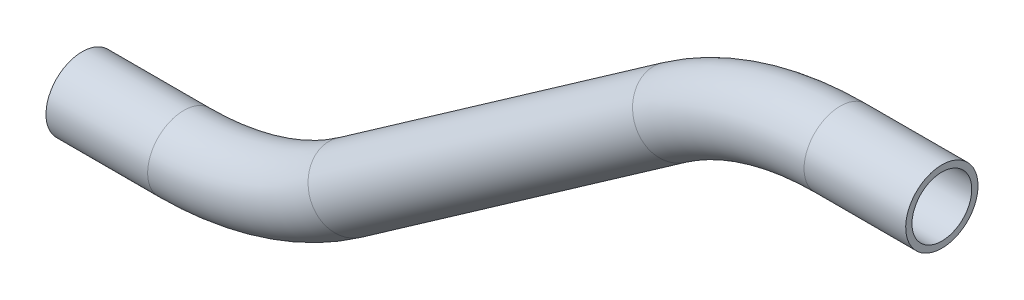
SolidWorks part; units mm, degrees
material "6061 Alloy"
ref_plane "Front Plane" through (0, 0, 0) normal (0, 0, 1) x (1, 0, 0)
ref_plane "Top Plane" through (0, 0, 0) normal (0, 1, 0) x (1, 0, 0)
ref_plane "Right Plane" through (0, 0, 0) normal (1, 0, 0) x (0, 0, -1)
sketch "Sketch4" plane through (0, 0, 0) normal (0, 0, 1) x (1, 0, 0)
  line L0 (95.0917, 47.4325) -> (121.8659, 47.4325)
  line L2 (51.3852, 33.6519) -> (-34.0921, -26.1999)
  line L3 (-34.0921, -26.1999) -> (71.0659, 47.4325)
  line L4 (121.8659, 47.4325) -> (71.0659, 47.4325)
  line L5 (-77.7986, -39.9805) -> (-104.5728, -39.9805)
  line L6 (-104.5728, -39.9805) -> (-53.7728, -39.9805)
  line L7 (51.3852, 33.6519) -> (-53.7728, -39.9805)
  arc A0 (95.0917, 47.4325) -> (51.3852, 33.6519) centre (95.0917, -28.7675) ccw
  arc A1 (-34.0921, -26.1999) -> (-77.7986, -39.9805) centre (-77.7986, 36.2195) cw
  point P9 (71.0659, 47.4325)
  point P14 (-53.7728, -39.9805)
  dimension "D3" = 35
  dimension "D4" = 35
  dimension "D1" = 76.2
  dimension "D2" = 76.2
  dimension "D5" = 152.4
  dimension "D6" = 50.8
  dimension "D7" = 50.8
ref_plane "Plane2" through (121.8659, 47.4325, 0) normal (-1, 0, 0) x (0, 0, 1)
sketch "Sketch5" plane through (121.8659, 47.4325, 0) normal (-1, 0, 0) x (0, 0, 1)
  circle A0 centre (0, 0) radius 9.525
  circle A1 centre (0, 0) radius 7.874
  dimension "D1" = 15.748
  dimension "D2" = 19.05
sweep "Sweep1" add profiles "Sketch5" path "Sketch4"
sketch "Sketch6" plane through (-104.5728, 0, 0) normal (-1, 0, 0) x (0, 0, 1)
  line L0 (-7.874, -39.9805) -> (7.874, -39.9805) construction
sketch "Sketch7" plane through (0, 0, 0) normal (0, 0, 1) x (1, 0, 0)
  line L0 (-104.5728, -39.9805) -> (-136.2487, -39.9805) construction
  line L1 (-104.5728, -30.4555) -> (-104.5728, -49.5055) construction
